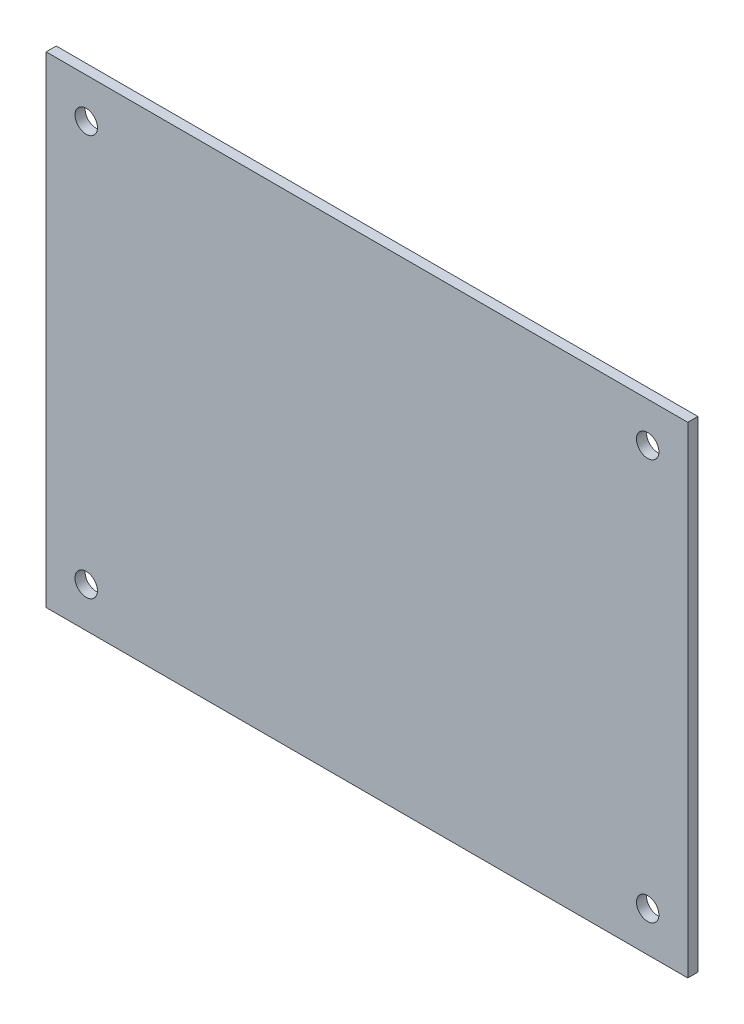
SolidWorks part; units mm, degrees
ref_plane "Front" through (0, 0, 0) normal (0, 0, 1) x (1, 0, 0)
ref_plane "Top" through (0, 0, 0) normal (0, 1, 0) x (1, 0, 0)
ref_plane "Right" through (0, 0, 0) normal (1, 0, 0) x (0, 0, -1)
sketch "Sketch1" plane through (0, 0, 0) normal (0, 0, 1) x (1, 0, 0)
  line L1 (0, 0) -> (101.6, 0)
  line L2 (0, 0) -> (0, -76.2)
  line L3 (0, -76.2) -> (101.6, -76.2)
  line L4 (101.6, 0) -> (101.6, -76.2)
  dimension "D1" = 101.6
  dimension "D2" = 76.2
extrude "Extrude1" add sketch "Sketch1" along normal blind 1.6002
sketch "Sketch2" plane through (0, 0, 1.6002) normal (0, 0, 1) x (1, 0, 0)
  line L0 (0, -76.2) -> (101.6, -76.2) construction
  line L1 (0, 0) -> (0, -76.2) construction
  circle A0 centre (6.35, -69.85) radius 1.778
  dimension "D1" = 3.556
  dimension "D2" = 6.35
  dimension "D3" = 6.35
extrude "Cut-Extrude1" cut sketch "Sketch2" against normal blind 1.6002
pattern_linear "LPattern1" count 2 spacing 63.5 count 2 spacing 88.9
